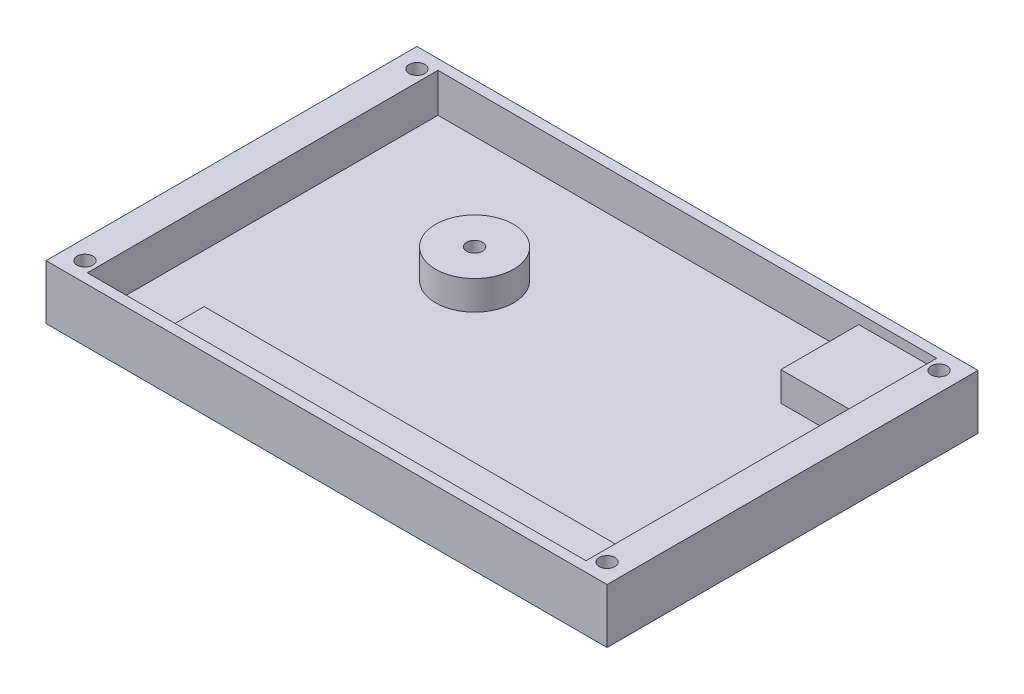
SolidWorks part; units mm, degrees
ref_plane "Front Plane" through (0, 0, 0) normal (0, 0, 1) x (1, 0, 0)
ref_plane "Top Plane" through (0, 0, 0) normal (0, 1, 0) x (1, 0, 0)
ref_plane "Right Plane" through (0, 0, 0) normal (1, 0, 0) x (0, 0, -1)
sketch "Sketch1" plane through (0, 0, 0) normal (0, 1, 0) x (1, 0, 0)
  line L1 (45.72, 30.226) -> (-45.72, 30.226)
  line L2 (45.72, 30.226) -> (45.72, -30.226)
  line L3 (45.72, -30.226) -> (-45.72, -30.226)
  line L4 (-45.72, 30.226) -> (-45.72, -30.226)
  line L5 (45.72, 30.226) -> (-45.72, -30.226) construction
  line L6 (45.72, -30.226) -> (-45.72, 30.226) construction
  point P0 (0, 0)
  dimension "D1" = 60.452
  dimension "D2" = 91.44
extrude "Boss-Extrude1" add sketch "Sketch1" along normal blind 8.89
sketch "Sketch2" plane through (0, 8.89, 0) normal (0, 1, 0) x (1, 0, 0)
  line L1 (40.64, 28.575) -> (-40.64, 28.575)
  line L2 (40.64, 28.575) -> (40.64, -28.575)
  line L3 (40.64, -28.575) -> (-40.64, -28.575)
  line L4 (-40.64, 28.575) -> (-40.64, -28.575)
  line L5 (40.64, 28.575) -> (-40.64, -28.575) construction
  line L6 (40.64, -28.575) -> (-40.64, 28.575) construction
  line L7 (-45.72, -30.226) -> (45.72, -30.226) construction
  point P0 (0, 0)
  dimension "D1" = 57.15
  dimension "D2" = 81.28
  dimension "D3" = 1.651
extrude "Cut-Extrude1" cut sketch "Sketch2" against normal blind 1.6002
sketch "Sketch3" plane through (0, 7.2898, 0) normal (0, 1, 0) x (1, 0, 0)
  line L1 (-40.64, 28.575) -> (27.94, 28.575)
  line L2 (-40.64, 28.575) -> (-40.64, -22.225)
  line L3 (-27.94, -22.225) -> (40.64, -22.225)
  line L4 (27.94, 28.575) -> (27.94, 15.875)
  line L5 (-40.64, -28.575) -> (40.64, -28.575) construction
  line L6 (27.94, 15.875) -> (40.64, 15.875)
  line L7 (-45.72, 30.226) -> (-45.72, -30.226) construction
  line L8 (-27.94, -22.225) -> (-27.94, -28.575)
  line L9 (-40.64, -28.575) -> (40.64, -28.575) construction
  line L10 (-27.94, -28.575) -> (-40.64, -28.575)
  line L11 (-40.64, -28.575) -> (-40.64, -22.225)
  line L12 (40.64, -28.575) -> (40.64, 28.575) construction
  line L13 (40.64, 15.875) -> (40.64, -22.225)
  circle A0 centre (-14.351, 8.255) radius 6.35
  circle A1 centre (-14.351, 8.255) radius 1.2891
  dimension "D3" = 12.7
  dimension "D4" = 2.5781
  dimension "D1" = 12.7
  dimension "D2" = 6.35
  dimension "D5" = 36.83
  dimension "D6" = 31.369
  dimension "D7" = 12.7
  dimension "D8" = 12.7
extrude "Cut-Extrude2" cut sketch "Sketch3" against normal offset from surface (4.7498 mm away) 2.54
sketch "Sketch4" plane through (0, 8.89, 0) normal (0, 1, 0) x (1, 0, 0)
  line L0 (45.72, 30.226) -> (-45.72, 30.226) construction
  line L1 (42.545, 27.051) -> (-42.545, 27.051) construction
  line L2 (42.545, 27.051) -> (42.545, -27.051) construction
  line L3 (42.545, -27.051) -> (-42.545, -27.051) construction
  line L4 (-42.545, 27.051) -> (-42.545, -27.051) construction
  line L5 (42.545, 27.051) -> (-42.545, -27.051) construction
  line L6 (42.545, -27.051) -> (-42.545, 27.051) construction
  line L7 (-45.72, 30.226) -> (-45.72, -30.226) construction
  circle A0 centre (-42.545, 27.051) radius 1.2891
  circle A1 centre (-42.545, -27.051) radius 1.2891
  circle A2 centre (42.545, -27.051) radius 1.2891
  circle A3 centre (42.545, 27.051) radius 1.2891
  point P0 (0, 0)
  dimension "D1" = 2.5781
  dimension "D2" = 3.175
  dimension "D3" = 3.175
extrude "Cut-Extrude3" cut sketch "Sketch4" against normal through all
